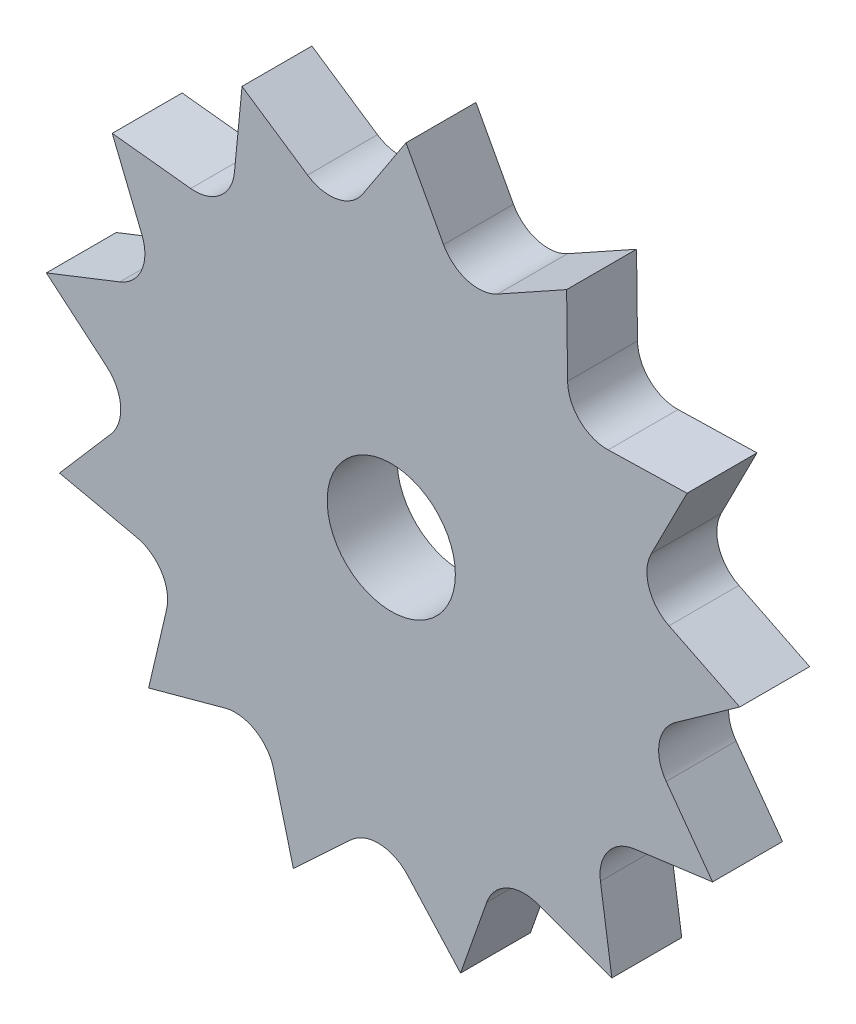
SolidWorks part; units mm, degrees
ref_plane "Front Plane" through (0, 0, 0) normal (0, 0, 1) x (1, 0, 0)
ref_plane "Top Plane" through (0, 0, 0) normal (0, 1, 0) x (1, 0, 0)
ref_plane "Right Plane" through (0, 0, 0) normal (1, 0, 0) x (0, 0, -1)
sketch "Sketch1" plane through (0, 0, 0) normal (0, 0, 1) x (1, 0, 0)
  circle A0 centre (0, 0) radius 15
  dimension "D1" = 30
extrude "Boss-Extrude1" add sketch "Sketch1" along normal blind 3
sketch "Sketch2" plane through (0, 0, 3) normal (0, 0, 1) x (1, 0, 0)
  circle A0 centre (0, 0) radius 2.75
  dimension "D1" = 5.5
extrude "Cut-Extrude1" cut sketch "Sketch2" against normal blind 11
sketch "Sketch3" plane through (0, 0, 3) normal (0, 0, 1) x (1, 0, 0)
  circle A0 centre (3.7387, 12.8158) radius 1.7
  dimension "D1" = 3.4
extrude "Cut-Extrude5" cut sketch "Sketch3" against normal blind 10
pattern_circular "CirPattern1" count 13 over 360 about axis through (0, 0, 0) along (0, 0, 1) of "Cut-Extrude5"
sketch "Sketch4" plane through (0, 0, 3) normal (0, 0, 1) x (1, 0, 0)
  line L0 (-1.2233, 12.1537) -> (0.6327, 14.9867)
  line L1 (0.6327, 14.9867) -> (2.2433, 12.0073)
  line L2 (2.2433, 12.0073) -> (4.8167, 13.9809)
  line L3 (4.8167, 13.9809) -> (-0.3494, 17.3394)
  line L4 (-0.3494, 17.3394) -> (-3.8666, 14.0723)
  line L5 (-3.8666, 14.0723) -> (-1.2233, 12.1537)
  arc A1 (3.7826, 14.5152) -> (-2.5459, 14.7824) centre (0, 0) ccw construction
  arc A3 (-3.3962, 14.6105) -> (-2.5459, 14.7824) centre (-2.6453, 13.0853) ccw construction
  arc A4 (3.7826, 14.5152) -> (4.6155, 14.2723) centre (3.7387, 12.8158) ccw construction
  point P8 (0, 0)
  point P16 (0, 0)
  point P17 (0, 0)
  point P18 (0, 0)
  point P19 (-0.3494, 17.3394)
extrude "Cut-Extrude6" cut sketch "Sketch4" against normal blind 10
pattern_circular "CirPattern2" count 13 over 360 about axis through (0, 0, 0) along (0, 0, 1) of "Cut-Extrude6"
